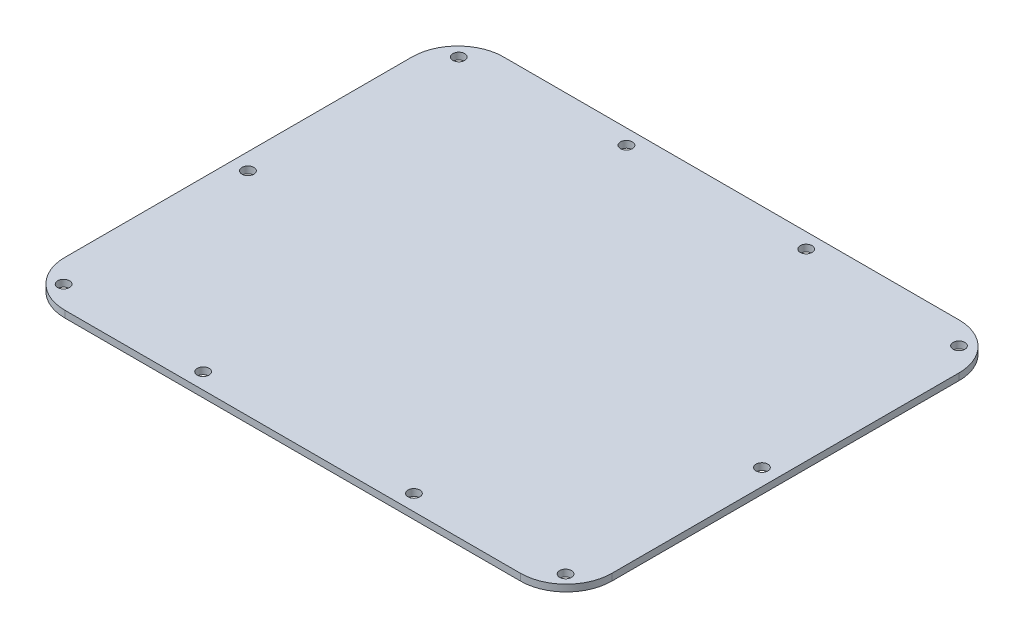
SolidWorks part; units mm, degrees
ref_plane "Front Plane" through (0, 0, 0) normal (0, 0, 1) x (1, 0, 0)
ref_plane "Top Plane" through (0, 0, 0) normal (0, 1, 0) x (1, 0, 0)
ref_plane "Right Plane" through (0, 0, 0) normal (1, 0, 0) x (0, 0, -1)
sketch "Sketch2" plane through (0, 0, 0) normal (0, 1, 0) x (1, 0, 0)
  line L0 (0, 0) -> (0, 207.7092) construction
  line L1 (-106.7689, -102.8065) -> (106.7689, -102.8065)
  line L2 (-128.2065, -81.3689) -> (-128.2065, 81.3689)
  line L3 (-106.7689, 102.8065) -> (106.7689, 102.8065)
  line L4 (128.2065, -81.3689) -> (128.2065, 81.3689)
  line L5 (-128.2065, -102.8065) -> (128.2065, 102.8065) construction
  line L6 (-128.2065, 102.8065) -> (128.2065, -102.8065) construction
  line L7 (0, 207.7092) -> (0, -151.1165) construction
  arc A0 (-106.7689, -102.8065) -> (-128.2065, -81.3689) centre (-106.7689, -81.3689) cw
  arc A1 (106.7689, -102.8065) -> (128.2065, -81.3689) centre (106.7689, -81.3689) ccw
  arc A2 (106.7689, 102.8065) -> (128.2065, 81.3689) centre (106.7689, 81.3689) cw
  arc A3 (-128.2065, 81.3689) -> (-106.7689, 102.8065) centre (-106.7689, 81.3689) cw
  circle A4 centre (42.1132, 95.7453) radius 2.7813
  circle A5 centre (117.221, 92.2909) radius 2.7813
  circle A6 centre (120.4468, -3.3147) radius 2.7813
  circle A7 centre (117.6274, -92.5195) radius 2.7813
  circle A8 centre (49.403, -95.3643) radius 2.7813
  circle A9 centre (-49.403, -95.3643) radius 2.7813
  circle A10 centre (-117.6274, -92.5195) radius 2.7813
  circle A11 centre (-120.4468, -3.3147) radius 2.7813
  circle A12 centre (-117.221, 92.2909) radius 2.7813
  circle A13 centre (-42.1132, 95.7453) radius 2.7813
  point P0 (0, 0)
  point P31 (0, 0)
  dimension "D3" = 21.4376
  dimension "D4" = 5.5626
  dimension "D7" = 5.5626
  dimension "D10" = 5.5626
  dimension "D13" = 5.5626
  dimension "D16" = 5.5626
  dimension "D1" = 205.613
  dimension "D2" = 256.413
  dimension "D5" = 42.1132
  dimension "D6" = 7.0612
  dimension "D8" = 117.221
  dimension "D9" = 10.5156
  dimension "D11" = 120.4468
  dimension "D12" = 106.1212
  dimension "D14" = 195.326
  dimension "D15" = 117.6274
  dimension "D17" = 7.4422
  dimension "D18" = 49.403
extrude "Boss-Extrude1" add sketch "Sketch2" along normal blind 3.175
